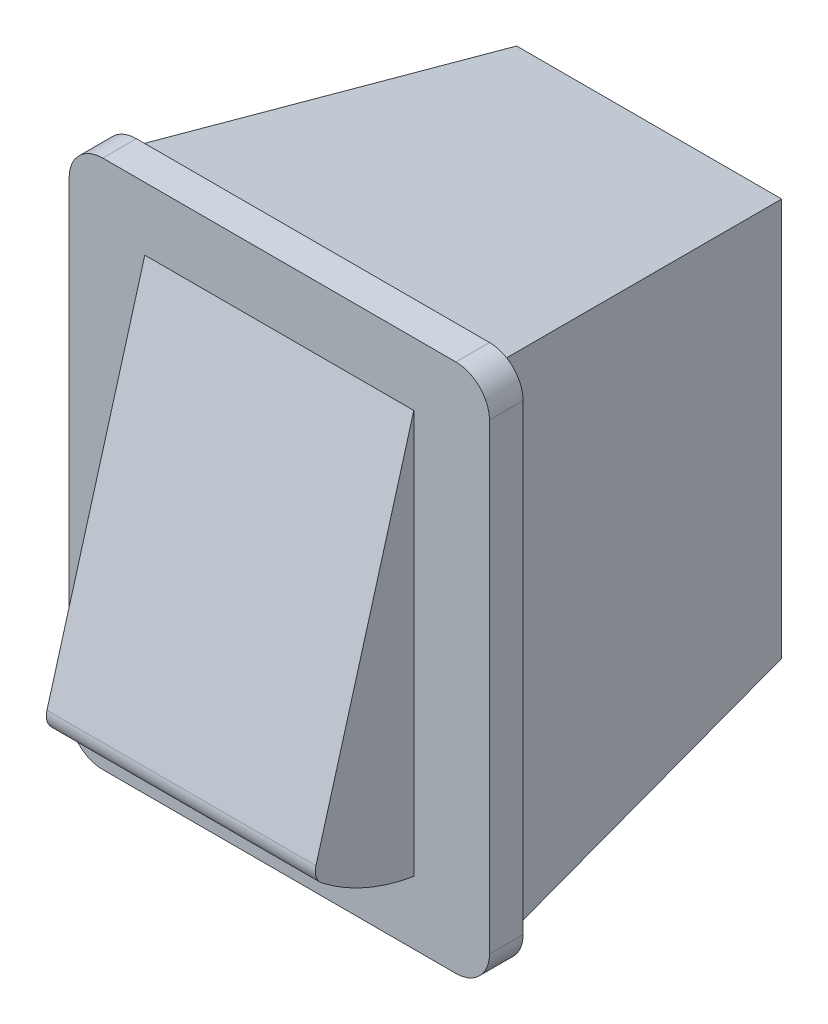
SolidWorks part; units mm, degrees
material "ABS"
ref_plane "Front Plane" through (0, 0, 0) normal (0, 0, 1) x (1, 0, 0)
ref_plane "Top Plane" through (0, 0, 0) normal (0, 1, 0) x (1, 0, 0)
ref_plane "Right Plane" through (0, 0, 0) normal (1, 0, 0) x (0, 0, -1)
sketch "Sketch1" plane through (0, 0, 0) normal (0, 0, 1) x (1, 0, 0)
  line L0 (0, 15.9009) -> (0, -18.375) construction
  line L1 (-10.5, -15.75) -> (10.5, -15.75)
  line L2 (-12.5, -13.75) -> (-12.5, 13.75)
  line L3 (-10.5, 15.75) -> (10.5, 15.75)
  line L4 (12.5, -13.75) -> (12.5, 13.75)
  line L5 (-12.5, -15.75) -> (12.5, 15.75) construction
  line L6 (-12.5, 15.75) -> (12.5, -15.75) construction
  line L7 (-17.1379, 0) -> (18.1638, 0) construction
  arc A0 (10.5, 15.75) -> (12.5, 13.75) centre (10.5, 13.75) cw
  arc A1 (10.5, -15.75) -> (12.5, -13.75) centre (10.5, -13.75) ccw
  arc A2 (-10.5, -15.75) -> (-12.5, -13.75) centre (-10.5, -13.75) cw
  arc A3 (-12.5, 13.75) -> (-10.5, 15.75) centre (-10.5, 13.75) cw
  point P0 (0, 0)
  dimension "D3" = 2
  dimension "D1" = 25
  dimension "D2" = 31.5
extrude "Boss-Extrude1" add sketch "Sketch1" along normal blind 2 contours L4 A0 L3 A3 L2 A2 L1 A1
sketch "Sketch2" plane through (0, 0, 0) normal (1, 0, 0) x (0, 0, -1)
  line L0 (-2, 12.0004) -> (-2, -12.0004)
  line L1 (-2, -13.75) -> (-2, 13.75) construction
  line L2 (-2, 12.0004) -> (-7.8219, -8.5375)
  line L3 (0, -13.75) -> (0, 13.75) construction
  arc A0 (-7.4742, -9.5992) -> (-2, -12.0004) centre (0, 0) ccw
  arc A1 (-7.8219, -8.5375) -> (-7.4742, -9.5992) centre (-6.8598, -8.8102) ccw
  point P1 (-2, 0)
  point P10 (-8, -9.1656)
  dimension "D3" = 1
  dimension "D1" = 22
  dimension "D2" = 8
extrude "Boss-Extrude2" add sketch "Sketch2" along normal mid plane 16
sketch "Sketch3" plane through (0, 0, 0) normal (0, 0, -1) x (-1, 0, 0)
  line L1 (-11.05, -15) -> (11.05, -15)
  line L2 (-11.05, -15) -> (-11.05, 15)
  line L3 (-11.05, 15) -> (11.05, 15)
  line L4 (11.05, -15) -> (11.05, 15)
  line L5 (-11.05, -15) -> (11.05, 15) construction
  line L6 (-11.05, 15) -> (11.05, -15) construction
  point P0 (0, 0)
  dimension "D1" = 22.1
  dimension "D2" = 30
extrude "Boss-Extrude3" add sketch "Sketch3" along normal blind 20 draft 9
